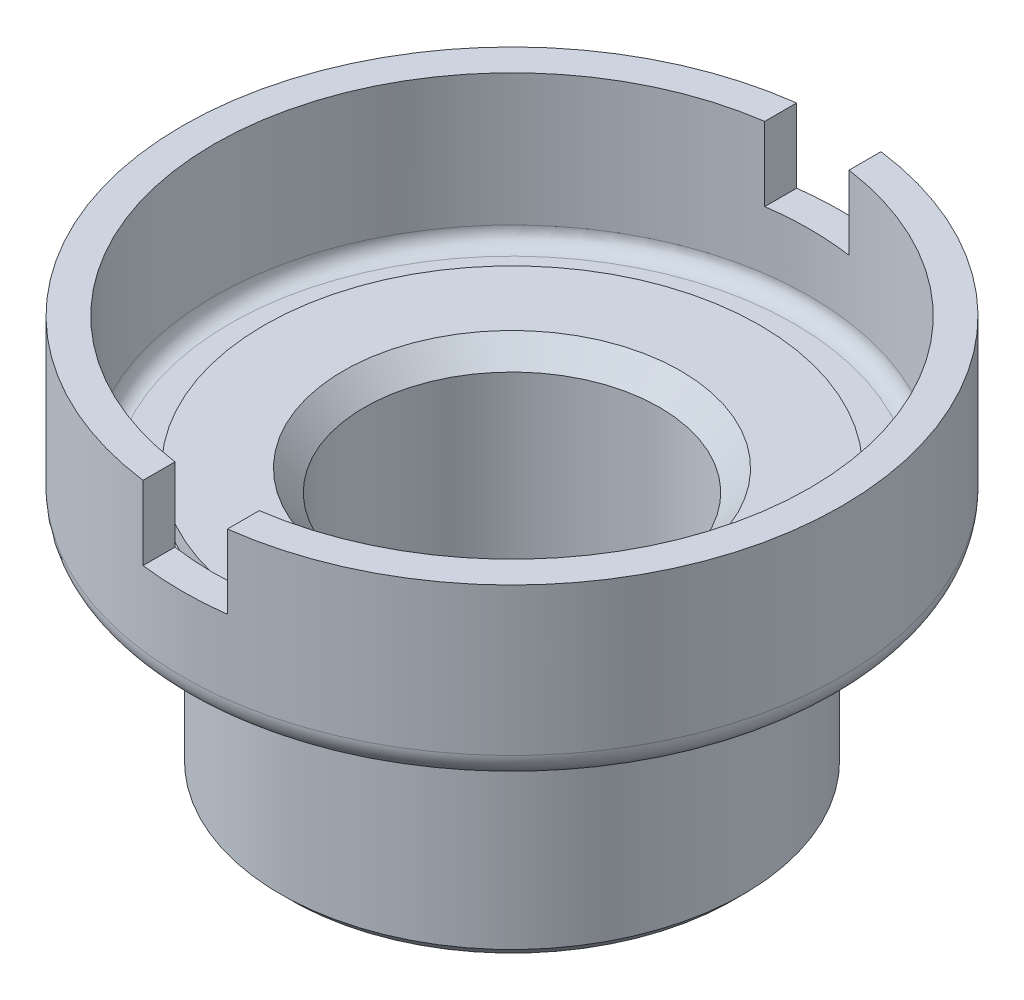
SolidWorks part; units mm, degrees
material "Stainless Steel (ferritic)"
ref_plane "Front Plane" through (0, 0, 0) normal (0, 0, 1) x (1, 0, 0)
ref_plane "Top Plane" through (0, 0, 0) normal (0, 1, 0) x (1, 0, 0)
ref_plane "Right Plane" through (0, 0, 0) normal (1, 0, 0) x (0, 0, -1)
sketch "Sketch1" plane through (0, 0, 0) normal (0, 0, 1) x (1, 0, 0)
  line L0 (0, 0) -> (0, 83.3171) construction
  line L1 (-28, 0) -> (-28, 46)
  line L2 (-32, 50) -> (-47, 50)
  line L3 (-47, 50) -> (-47, 47)
  line L4 (-47, 47) -> (-53.5, 47)
  line L5 (-56.5, 50) -> (-56.5, 75)
  line L6 (-56.5, 75) -> (-62.5, 75)
  line L7 (-62.5, 75) -> (-62.5, 47)
  line L8 (-57.5, 42) -> (-43.94, 42)
  line L9 (-43.94, 42) -> (-43.94, 2)
  line L10 (-41.94, 0) -> (-28, 0)
  line L11 (-28, 46) -> (-32, 50)
  line L12 (-43.94, 2) -> (-41.94, 0)
  arc A0 (-62.5, 47) -> (-57.5, 42) centre (-57.5, 47) ccw
  arc A1 (-53.5, 47) -> (-56.5, 50) centre (-53.5, 50) cw
  point P4 (-28, 50)
  point P13 (-43.94, 0)
  point P20 (-62.5, 42)
  dimension "D14" = 5
  dimension "D15" = 3
  dimension "D1" = 28
  dimension "D2" = 43.94
  dimension "D3" = 47
  dimension "D4" = 3
  dimension "D5" = 62.5
  dimension "D6" = 56.5
  dimension "D7" = 50
  dimension "D8" = 42
  dimension "D9" = 75
  dimension "D10" = 4
  dimension "D11" = 45
  dimension "D12" = 2
  dimension "D13" = 45
revolve "Revolve1" add sketch "Sketch1" angle 360 about L0
sketch "Sketch2" plane through (0, 0, 0) normal (0, 0, 1) x (1, 0, 0)
  line L0 (62.5, 75) -> (-62.5, 75) construction
  line L1 (-8, 75) -> (8, 75)
  line L2 (-8, 75) -> (-8, 61)
  line L3 (-8, 61) -> (8, 61)
  line L4 (8, 75) -> (8, 61)
  point P6 (0, 61)
  dimension "D1" = 16
  dimension "D2" = 14
extrude "Cut-Extrude1" cut sketch "Sketch2" against normal mid plane 221
